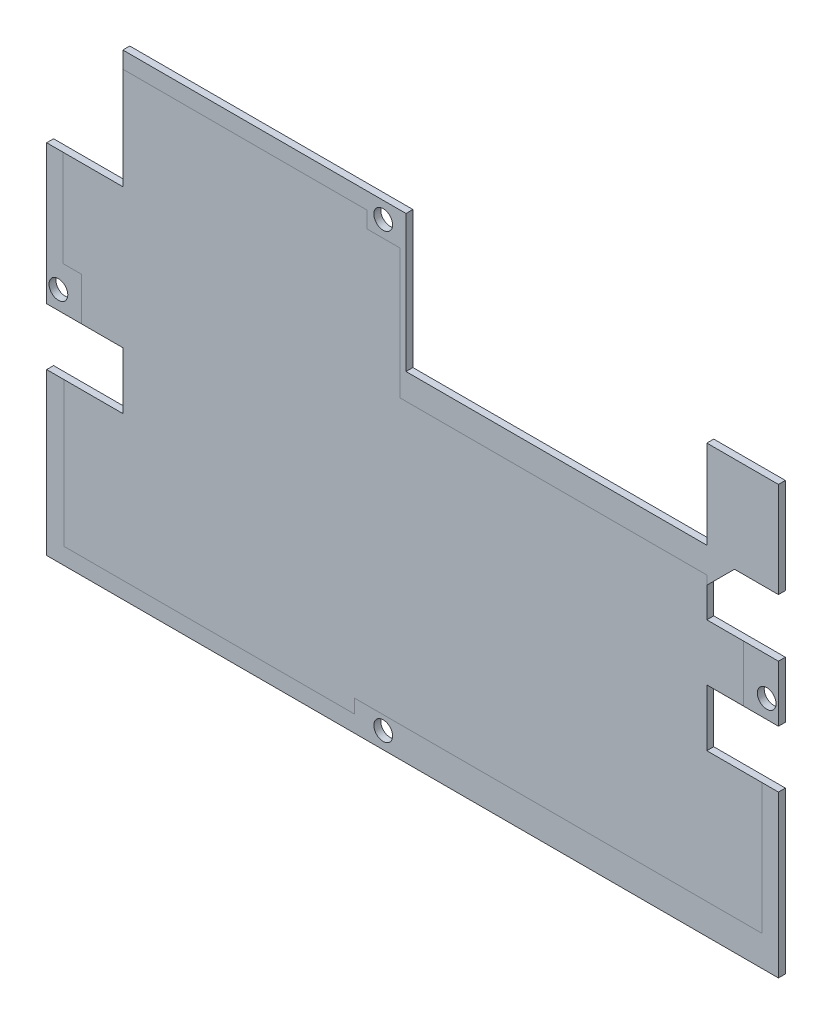
SolidWorks part; units mm, degrees
ref_plane "Front Plane" through (0, 0, 0) normal (0, 0, 1) x (1, 0, 0)
ref_plane "Top Plane" through (0, 0, 0) normal (0, 1, 0) x (1, 0, 0)
ref_plane "Right Plane" through (0, 0, 0) normal (1, 0, 0) x (0, 0, -1)
sketch "Sketch1" plane through (0, 0, 0) normal (0, 0, 1) x (1, 0, 0)
  line L0 (9.878, 12.192) -> (9.878, -93.472) construction
  line L1 (-41.367, 14.097) -> (6.6634, 14.097)
  line L2 (-41.367, 14.097) -> (-41.367, -13.0805)
  line L3 (-38.029, -95.123) -> (9.878, -95.123)
  line L4 (91.388, 14.5) -> (91.388, -20.5) construction
  line L5 (-41.367, 14.097) -> (9.878, -95.123) construction
  line L6 (-38.029, -95.123) -> (6.6634, 14.097) construction
  line L8 (-38.029, -95.123) -> (-58.8607, -95.123)
  line L10 (-41.367, -58.1655) -> (-58.8607, -58.1655)
  line L11 (-58.8607, -95.123) -> (-58.8607, -58.1655)
  line L12 (-38.029, -95.123) -> (-58.8607, -58.1655) construction
  line L13 (-41.367, -58.1655) -> (-58.8607, -95.123) construction
  line L14 (9.878, -95.123) -> (90.0829, -95.123)
  line L15 (99.008, -18.923) -> (109.0968, -18.923)
  line L16 (23.618, -17.32) -> (92.658, -17.32)
  line L17 (92.658, -58.1655) -> (92.658, -45.0855)
  line L18 (9.878, -95.123) -> (92.658, -17.32) construction
  line L19 (7.5194, -20.856) -> (90.0829, -95.123) construction
  line L20 (24.888, -20.5) -> (24.888, 14.5) construction
  line L21 (6.6634, 14.097) -> (23.618, 14.097)
  line L22 (92.658, -17.32) -> (92.658, 2.9845)
  line L23 (92.658, 2.9845) -> (109.0968, 2.9845)
  line L24 (23.618, 14.097) -> (23.618, -17.32)
  line L25 (6.6634, 14.097) -> (23.618, -17.32) construction
  line L26 (6.8209, -14.9887) -> (23.618, 14.097) construction
  line L27 (109.0968, -18.923) -> (109.0968, 2.9845)
  line L28 (90.0829, -95.123) -> (109.0968, -95.123)
  line L29 (92.658, -10.8044) -> (109.0968, 2.9845) construction
  line L30 (92.658, -58.1655) -> (109.0968, -58.1655)
  line L31 (109.0968, -95.123) -> (109.0968, -58.1655)
  line L32 (90.0829, -95.123) -> (109.0968, -58.1655) construction
  line L33 (92.658, -58.1655) -> (109.0968, -95.123) construction
  line L34 (92.658, 2.9845) -> (109.0968, -18.923) construction
  line L35 (99.008, -18.923) -> (92.658, -25.273)
  line L36 (89.888, -16.05) -> (26.388, -16.05) construction
  line L38 (-58.8607, -13.0805) -> (-41.367, -13.0805)
  line L39 (-58.8607, -13.0805) -> (-58.8607, -45.0855)
  line L40 (-58.8607, -45.0855) -> (-41.367, -45.0855)
  line L42 (-58.8607, -13.0805) -> (-41.367, -45.0855) construction
  line L43 (-58.8607, -45.0855) -> (-41.367, -13.0805) construction
  line L44 (-41.367, -45.0855) -> (-41.367, -58.1655)
  line L45 (111.6368, -97.663) -> (-61.4007, -97.663) construction
  line L46 (-44.732, 16.637) -> (94.968, 16.637) construction
  line L47 (-43.907, -8.6021) -> (-43.907, -4.4789) construction
  line L48 (-45.8454, -10.5405) -> (-49.9686, -10.5405) construction
  line L49 (-61.4007, -97.663) -> (-61.4007, 5.5245) construction
  line L50 (-45.8454, -47.6255) -> (-49.9686, -47.6255) construction
  line L51 (-45.8454, -55.6255) -> (-49.9686, -55.6255) construction
  line L52 (100.048, 5.5245) -> (111.6368, 5.5245) construction
  line L53 (111.6368, 5.5245) -> (111.6368, -97.663) construction
  line L54 (101.4746, -55.6255) -> (97.3514, -55.6255) construction
  line L55 (101.4746, -47.6255) -> (97.3514, -47.6255) construction
  line L56 (92.658, -32.1509) -> (109.0968, -32.1509)
  line L58 (92.658, -45.0855) -> (109.0968, -45.0855)
  line L59 (109.0968, -32.1509) -> (109.0968, -45.0855)
  line L60 (92.658, -32.1509) -> (109.0968, -45.0855) construction
  line L61 (92.658, -45.0855) -> (109.0968, -32.1509) construction
  line L62 (92.658, -32.1509) -> (92.658, -25.273)
  point P4 (-15.7115, -40.5833)
  point P12 (-49.352, -75.0348)
  point P17 (49.1005, -58.2587)
  point P26 (14.8536, -1.0794)
  point P32 (100.2804, -75.3021)
  point P38 (99.008, -5.478)
  point P52 (-50.1139, -29.083)
  point P76 (100.8774, -38.6182)
  dimension "D4" = 45
  dimension "D1" = 1.27
  dimension "D2" = 1.27
  dimension "D5" = 1.27
  dimension "D6" = 2.54
  dimension "D7" = 2.54
  dimension "D8" = 2.54
  dimension "D9" = 2.54
  dimension "D10" = 2.54
  dimension "D11" = 2.54
  dimension "D12" = 2.54
  dimension "D13" = 2.54
  dimension "D14" = 2.54
  dimension "D15" = 2.54
  dimension "D17" = 2.54
  dimension "D18" = 2.54
  dimension "D19" = 6.35
extrude "Boss-Extrude1" add sketch "Sketch1" along normal blind 1.5875 contours L1 L21 L24 L16 L22 L23 L27 L15 L35 L62 L56 L59 L58 L17 L30 L31 L28 L14 L3 L8 L11 L10 L44 L40 L39 L38 L2
hole_wizard "#6 Clearance Hole1" positions "Sketch3" profile "Sketch2" hole size "#6" standard "ANSI Inch" end condition through all
sketch "Sketch3" plane through (0, 0, 0) normal (0, 0, -1) x (-1, 0, 0)
  point P0 (-106.398, -40.894)
  point P2 (-18.387, 10.287)
  point P4 (56.162, -40.894)
  point P6 (-18.387, -91.313)
sketch "Sketch2" plane through (106.398, -40.894, 0) normal (1, 0, 0) x (0, 1, 0)
  line L0 (0, 0) -> (0, 1.5875)
  line L1 (0, 1.5875) -> (2.1526, 1.5875)
  line L2 (2.1526, 1.5875) -> (2.1526, 0)
  line L5 (2.1526, 0) -> (0, 0)
  line L11 (0, -6.35) -> (0, 107.95) construction
  dimension "Thru Hole Dia." = 4.3053
  dimension "Thru Hole Depth" = 1.5875
sketch "Sketch4" plane through (0, 0, 1.5875) normal (0, 0, 1) x (1, 0, 0)
  line L0 (-41.367, 10.287) -> (14.6198, 10.287)
  line L1 (-41.367, 14.097) -> (-41.367, -13.0805) construction
  line L2 (14.6198, 10.287) -> (14.6198, 6.5468)
  line L3 (14.6198, 6.5468) -> (22.2764, 6.5468)
  line L4 (22.2764, 6.5468) -> (22.2764, -23.243)
  line L5 (22.2764, -23.243) -> (92.7226, -23.243)
  line L6 (92.7226, -23.243) -> (92.658, -32.1509)
  line L7 (92.658, -32.1509) -> (101.0599, -32.1509)
  line L8 (101.0599, -32.1509) -> (101.0599, -45.0385)
  line L9 (101.0599, -45.0385) -> (92.658, -45.0855)
  line L10 (92.658, -45.0855) -> (92.658, -58.1655)
  line L11 (92.658, -58.1655) -> (105.3245, -58.1655)
  line L12 (105.3245, -58.1655) -> (105.2868, -88.138)
  line L13 (105.2868, -88.138) -> (11.7894, -88.138)
  line L14 (11.7894, -88.138) -> (11.7894, -91.313)
  line L15 (11.7894, -91.313) -> (-54.9021, -91.313)
  line L16 (-54.9021, -91.313) -> (-54.9021, -58.1655)
  line L17 (-54.9021, -58.1655) -> (-41.367, -58.1655)
  line L18 (-41.367, -58.1655) -> (-41.367, -45.0855)
  line L19 (-41.367, -45.0855) -> (-50.8981, -45.0855)
  line L20 (-50.8981, -45.0855) -> (-50.8981, -35.2241)
  line L21 (-50.8981, -35.2241) -> (-55.1233, -35.2241)
  line L22 (-55.1233, -35.2241) -> (-55.1233, -13.0805)
  line L23 (-55.1233, -13.0805) -> (-41.367, -13.0805)
  line L24 (-41.367, -13.0805) -> (-41.367, 10.287)
split line "Split Line1"
